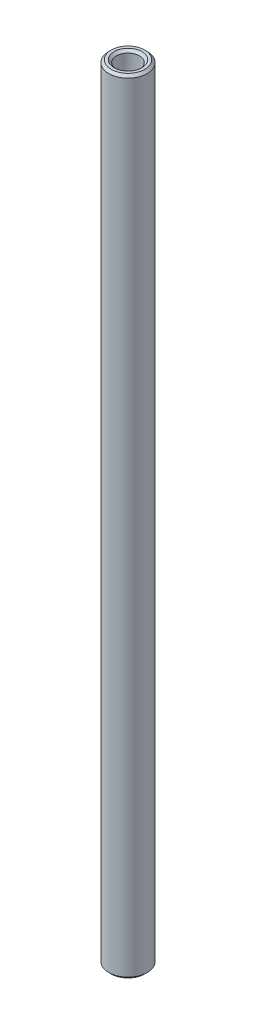
SolidWorks part; units mm, degrees
ref_plane "Front Plane" through (0, 0, 0) normal (0, 0, 1) x (1, 0, 0)
ref_plane "Top Plane" through (0, 0, 0) normal (0, 1, 0) x (1, 0, 0)
ref_plane "Right Plane" through (0, 0, 0) normal (1, 0, 0) x (0, 0, -1)
sketch "Sketch1" plane through (0, 0, 0) normal (0, 1, 0) x (1, 0, 0)
  circle A0 centre (0, 0) radius 1.9844
  circle A1 centre (0, 0) radius 1.1906
  dimension "D1" = 3.9688
  dimension "D2" = 0.7937
extrude "Boss-Extrude1" add sketch "Sketch1" along normal mid plane 80.9625
chamfer "Chamfer1" distance 0.254 angle 45 4 edges at (0, -40.4812, 1.1906) (0, -40.4812, 1.9844) (0, 40.4812, 1.1906) (0, 40.4812, 1.9844)
